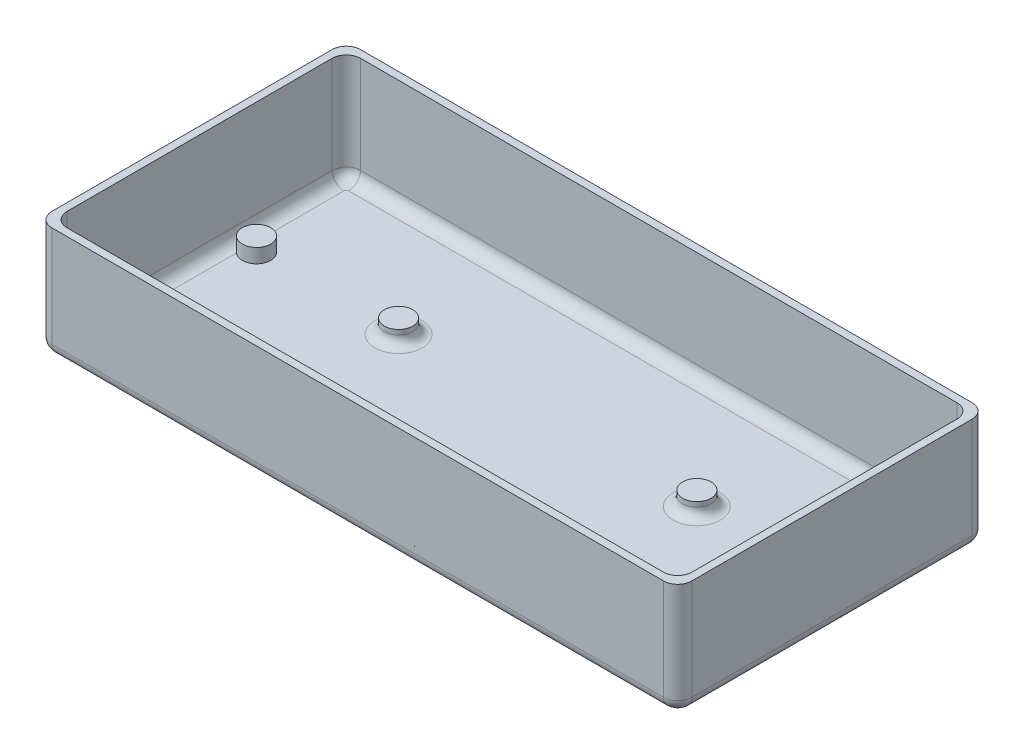
SolidWorks part; units mm, degrees
ref_plane "Спереди" through (0, 0, 0) normal (0, 0, 1) x (1, 0, 0)
ref_plane "Сверху" through (0, 0, 0) normal (0, 1, 0) x (1, 0, 0)
ref_plane "Справа" through (0, 0, 0) normal (1, 0, 0) x (0, 0, -1)
sketch "Sketch1" plane through (0, 0, 0) normal (0, 1, 0) x (1, 0, 0)
  line L0 (-67.6, -32.6) -> (-67.6, 32.6)
  line L1 (-66, -31) -> (66, -31)
  line L2 (-66, -31) -> (-66, 31)
  line L3 (-66, 31) -> (66, 31)
  line L4 (66, -31) -> (66, 31)
  line L5 (-66, -31) -> (66, 31) construction
  line L6 (-66, 31) -> (66, -31) construction
  line L7 (-67.6, 32.6) -> (67.6, 32.6)
  line L8 (67.6, -32.6) -> (67.6, 32.6)
  line L9 (-67.6, -32.6) -> (67.6, -32.6)
  point P0 (0, 0)
  dimension "D1" = 1.6
  dimension "D2" = 62
  dimension "D3" = 132
extrude "Boss-Extrude1" add sketch "Sketch1" along normal blind 23
sketch "Sketch2" plane through (0, 0, 0) normal (0, -1, 0) x (1, 0, 0)
  line L1 (-67.6, -32.6) -> (67.6, -32.6)
  line L2 (-67.6, -32.6) -> (-67.6, 32.6)
  line L3 (-67.6, 32.6) -> (67.6, 32.6)
  line L4 (67.6, -32.6) -> (67.6, 32.6)
  line L5 (-67.6, -32.6) -> (67.6, 32.6) construction
  line L6 (-67.6, 32.6) -> (67.6, -32.6) construction
  point P0 (0, 0)
extrude "Boss-Extrude2" add sketch "Sketch2" along normal blind 0.8
fillet "Fillet1" radius 3 8 edges at (67.6, 11.1, -32.6) (-67.6, 11.1, -32.6) (-67.6, 11.1, 32.6) (-66, 11.5, 31) (67.6, 11.1, 32.6) (66, 11.5, 31) (66, 11.5, -31) (-66, 11.5, -31)
fillet "Fillet2" radius 2.5 16 edges at (66.7213, -0.8, 31.7213) (67.6, -0.8, 0) (66.7213, -0.8, -31.7213) (0, -0.8, -32.6) (-66.7213, -0.8, -31.7213) (-67.6, -0.8, 0) (-66.7213, -0.8, 31.7213) (0, -0.8, 32.6) (-65.1213, 0, -30.1213) (0, 0, -31) (65.1213, 0, -30.1213) (66, 0, 0) (65.1213, 0, 30.1213) (0, 0, 31) (-65.1213, 0, 30.1213) (-66, 0, 0)
sketch "Sketch3" plane through (0, 0, 0) normal (0, 1, 0) x (1, 0, 0)
  circle A0 centre (-31.5, -26.5) radius 3
  circle A1 centre (-61.5, -26.5) radius 3
  circle A2 centre (31.5, -26.5) radius 3
  circle A3 centre (61.5, -26.5) radius 3
  circle A4 centre (-31.5, 7.5397) radius 3
  circle A5 centre (-61.5, 7.5397) radius 3
  circle A6 centre (31.5, 7.5397) radius 3
  circle A7 centre (61.5, 7.5397) radius 3
  point P20 (0, 0)
  point P21 (0, 0)
  point P22 (0, 0)
  point P23 (0, 0)
  dimension "D1" = 6
extrude "Boss-Extrude5" add sketch "Sketch3" along normal blind 3
sketch "Sketch4" plane through (0, 3, 0) normal (0, 1, 0) x (1, 0, 0)
  circle A0 centre (-61.5, -26.5) radius 1.4
  circle A1 centre (-31.5, -26.5) radius 1.4
  circle A2 centre (31.5, -26.5) radius 1.4
  circle A3 centre (61.5, -26.5) radius 1.4
extrude "Boss-Extrude6" add sketch "Sketch4" along normal blind 3
fillet "Fillet3" radius 0.8 4 edges at (61.5, 3, 27.9) (31.5, 3, 27.9) (-31.5, 3, 27.9) (-61.5, 3, 27.9)
fillet "Fillet4" radius 2 2 edges at (31.5, 0, -4.5397) (-31.5, 0, -4.5397)
